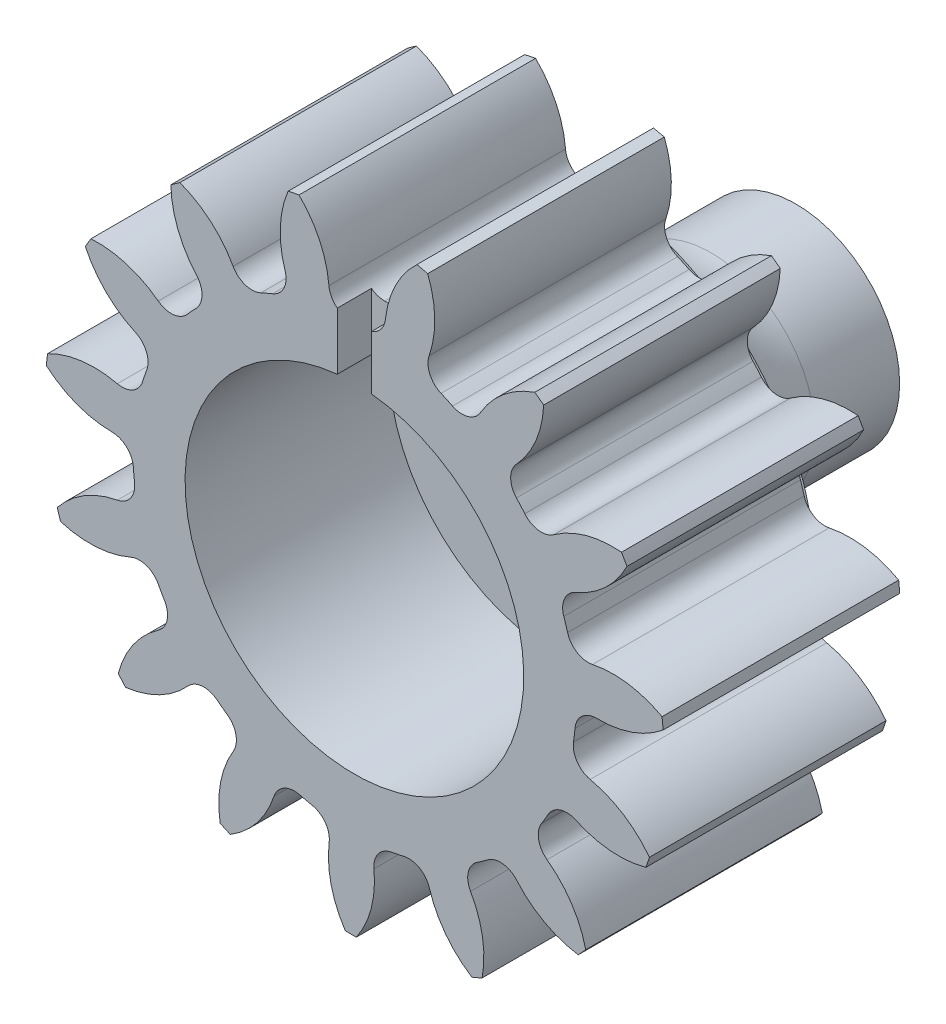
SolidWorks part; units mm, degrees
material "ABS"
ref_plane "Front" through (0, 0, 0) normal (0, 0, 1) x (1, 0, 0)
ref_plane "Top" through (0, 0, 0) normal (0, 1, 0) x (1, 0, 0)
ref_plane "Right" through (0, 0, 0) normal (1, 0, 0) x (0, 0, -1)
sketch "Sketch3" plane through (0, 0, 0) normal (0, 0, 1) x (1, 0, 0)
  circle A0 centre (0, 0) radius 21.59
  dimension "od" = 43.18
extrude "gearBody" add sketch "Sketch3" along normal blind 11
sketch "Sketch2" plane through (0, 0, 0) normal (0, 0, 1) x (1, 0, 0)
  line L0 (0, 0) -> (17.0393, 7.0579) construction
  line L1 (22.0105, -8.0941) -> (0, 0) construction
  line L2 (0, 0) -> (36.3143, 0) construction
  line L3 (19.0486, -0.229) -> (18.5878, -4.1711) construction
  line L5 (18.8182, -2.2) -> (0, 0) construction
  line L7 (0, 0) -> (18.4432, 0) construction
  arc A0 (18.4395, -0.3701) -> (18.0276, -3.8932) centre (0, 0) ccw construction
  arc A1 (21.5666, 1.0048) -> (20.7532, -5.9524) centre (0, 0) ccw construction
  arc A2 (19.0486, -0.229) -> (18.5878, -4.1711) centre (0, 0) ccw construction
  arc A3 (15.7838, -2.3046) -> (15.8898, -1.3984) centre (0, 0) ccw construction
  arc A4 (22.0105, -8.0941) -> (16.5506, -3.4102) centre (14.9518, -10.798) ccw construction
  arc A5 (22.0105, -8.0941) -> (23.2839, 2.7987) centre (0, 0) ccw construction
  arc A6 (23.2839, 2.7987) -> (16.8909, -0.4995) centre (17.0393, 7.0579) cw construction
  arc A7 (15.8898, -1.3984) -> (16.8909, -0.4995) centre (16.8715, -1.4848) cw construction
  arc A8 (16.5506, -3.4102) -> (15.7838, -2.3046) centre (16.759, -2.4469) cw construction
  arc A9 (23.5577, 4.3699) -> (16.9008, 0.0084) centre (17.0393, 7.0579) cw
  arc A10 (15.3837, -1.3539) -> (16.9008, 0.0084) centre (16.8715, -1.4848) cw
  arc A11 (15.2812, -2.2312) -> (15.3837, -1.3539) centre (0, 0) ccw
  arc A12 (16.4431, -3.9067) -> (15.2812, -2.2312) centre (16.759, -2.4469) cw
  arc A13 (21.9144, -9.686) -> (16.4431, -3.9067) centre (14.9518, -10.798) ccw
  arc A14 (21.9144, -9.686) -> (23.5577, 4.3699) centre (0, 0) ccw
  point P6 (23.2839, 2.7987)
  point P22 (22.0105, -8.0941)
  dimension "D1" = 0.508
  dimension "baseDia" = 36.8864
  dimension "od" = 43.18
  dimension "pd" = 38.1
  dimension "rd" = 31.9024
  dimension "rFillet" = 0.9855
  dimension "pointX" = 23.2839
  dimension "pointY" = 2.7987
  dimension "CTT" = 3.9421
  dimension "flankCenterAngle" = 22.5
extrude "toothCut" cut sketch "Sketch2" along normal through all
pattern_circular "CirPattern1" count 15 over 360 about axis through (0, 0, 0) along (0, 0, 1) of "toothCut"
scale "Scale1" scale about centroid uniform scaling no x scale factor 0.666667 y scale factor 0.666667 z scale factor 1
sketch "hub1Dia" plane through (0, 0, 0) normal (0, 0, -1) x (-1, 0, 0)
  circle A0 centre (0, 0) radius 12.7
  dimension "hub1Dia" = 25.4
sketch "hub2Dia" plane through (0, 0, 11) normal (0, 0, 1) x (1, 0, 0)
  circle A0 centre (0, 0) radius 12.7
  dimension "hub2dia" = 25.4
sketch "boreDia" plane through (0, 0, 0) normal (0, 0, 1) x (1, 0, 0)
  circle A0 centre (0, 0) radius 7.874
  dimension "boreDia" = 15.748
extrude "bore" cut sketch "boreDia" against normal mid plane 25400
sketch "Sketch4" plane through (0, 0, 0) normal (1, 0, 0) x (0, 0, -1)
  line L0 (9.525, 0) -> (-1.524, 0)
  line L1 (-1.524, 0) -> (-1.524, 7.874)
  line L2 (-1.524, 7.874) -> (0, 7.874)
  line L4 (0, 7.874) -> (0, 10.414)
  line L7 (5.588, 4.826) -> (9.525, 4.826)
  line L8 (9.525, 4.826) -> (9.525, 0)
  line L9 (0, 0) -> (18.4907, 0) construction
  line L11 (0, 8.3769) -> (0, 11.3894) construction
  arc A0 (0, 10.414) -> (5.588, 4.826) centre (5.588, 10.414) ccw
  point P10 (0, 0)
  point P13 (0, 0)
  dimension "D2" = 5.588
  dimension "D1" = 15.748
  dimension "D3" = 1.524
  dimension "D5" = 9.652
  dimension "D6" = 9.525
revolve "Revolve1" add sketch "Sketch4" angle 360 about L9
sketch "Sketch5" plane through (0, 0, -9.525) normal (0, 0, -1) x (-1, 0, 0)
  circle A0 centre (0, 0) radius 2.65
  dimension "D1" = 5.3
extrude "Cut-Extrude1" cut sketch "Sketch5" against normal blind 3.746
sketch "Sketch6" plane through (0, 0, -9.525) normal (0, 0, -1) x (-1, 0, 0)
  line L0 (0, 0) -> (0, 3.8857) construction
  line L1 (0.06, 3.0494) -> (0.23, 2.64)
  line L2 (-0.06, 3.0494) -> (-0.23, 2.64)
  circle A0 centre (0, 0) radius 2.65 construction
  arc A1 (0.23, 2.64) -> (-0.23, 2.64) centre (0, 0) ccw
  arc A2 (0.06, 3.0494) -> (-0.06, 3.0494) centre (0, 0) ccw
  dimension "D1" = 6.1
  dimension "D2" = 0.06
  dimension "D3" = 0.23
extrude "Cut-Extrude4" cut sketch "Sketch6" against normal blind 3.746
pattern_circular "CirPattern2" count 25 over 360 about axis through (0, 0, 0) along (0, 0, 1) of "Cut-Extrude4"
sketch "Sketch7" plane through (0, 0, 11) normal (0, 0, 1) x (1, 0, 0)
  line L1 (-0.7937, 13.1786) -> (0.7937, 13.1786)
  line L2 (-0.7937, 13.1786) -> (-0.7937, 5.7938)
  line L3 (-0.7937, 5.7938) -> (0.7937, 5.7938)
  line L4 (0.7937, 13.1786) -> (0.7937, 5.7938)
  point P4 (0, 5.7938)
  point P6 (0, 0)
  dimension "D1" = 1.5875
extrude "Cut-Extrude5" cut sketch "Sketch7" against normal blind 1.5875
equation "\"Motor_OD\" = 54.4mm"
equation "\"Motor_Length\" = 401mm"
equation "\"Aft_Section_Length\" = 32in"
equation "\"Mid_Coupler_Length\" = 12in"
equation "\"AB_Coupler_OD_Length\"= 1in"
equation "\"AB_Coupling_Section_Length\"= 0.375in"
equation "\"AB_Coupler_Length\"= \"AB_Coupler_OD_Length\" + \"AB_Coupling_Section_Length\" * 2"
equation "\"Cutout_Angle\" = 60"
equation "\"AB_Paddle_Height\" = 0.375in"
equation "\"AB_Coupler_Num_Screws\"= 4"
equation "\"Num_Cutouts\" = 4"
equation "\"AB_Coupler_OD\"= 4.024in"
equation "\"AB_Coupler_ID\"= 3.7in"
equation "\"AB_Coupler_Surface_Diameter\"= 3.899in"
equation "\"AB_Coupling_Screw_Diameter\"= 4.5mm"
equation "\"AB_Central_Bushing_Length\" = 0.75in"
equation "\"Lead_Screw_Dist\" = 2in"
equation "\"Lead_Screw_Diam\" = 0.375in"
equation "\"Lead_Screw_Length\" = \"Mid_Coupler_Length\" + 2*0.375in + 2*0.5in"
equation "\"Paddle_Pin_Offset\" = 0.25in"
equation "\"Paddle_Pin_Radius\" = 2.25*2/3in"
equation "\"Paddle_Gear_OD\" = 3.2in"
equation "\"Fwd_BKHD_From_Top\" = 18in"
equation "\"Body_Tube_OD\"= 4.024in"
equation "\"Body_Tube_ID\"= 3.90in"
equation "\"Coupler_OD\" = 3.899in"
equation "\"Coupler_ID\" = 3.755in"
equation "\"Fwd_Section_Length\" = 20in"
equation "\"Mid_Section_Length\" = 4in"
equation "\"Aft_Upper_Tube_Length\" = 10in"
equation "\"Aft_Lower_Tube_Length\" = 18in"
equation "\"Nosecone_Coupler_Length\" = 5in"
equation "\"Avionics_Bulkhead_Thickness\" = 0.25in"
equation "\"Avionics_Bulkhead_Lip\" = 0.125in"
equation "\"Avionics_Board_Length\" = \"Mid_Coupler_Length\" - 2*\"Avionics_Bulkhead_Lip\""
equation "\"Lead_Screw_Hole_Diam\" = 0.386in"
equation "\"Centering_Ring_Cutout_Dia\"= 1in"
equation "\"Fin_Thickness\" = 0.118in"
equation "\"Airbrakes_Wire_Hole_Dist\" = 1.1*2/3in"
equation "\"Airbrakes_Wire_Hole_Dia\" = 0.25in"
equation "\"Drive_Gear_OD\" = 1.7*2/3in"
equation "\"DB9_Hole_Dist\" = 25mm"
equation "\"DB9_Relief_Width\" = 0.47in"
equation "\"DB9_Relief_Hole_Offset\" = 0.09in"
equation "\"Servo_Gear_Offset\" = 0.5in"
equation "\"Mounting_Bracket_Centerhole_DIA\" = 0.4in"
equation "\"Drive_Gear_Shaft_DIA\" = \"Mounting_Bracket_Centerhole_DIA\" - 0.02in"
equation "\"Drive_Gear_Fillet\" = 0.22in"
equation "\"Drive_Gear_ID\" = 0.62in"
equation "\"M3_Thread_Clearance\" = 3.8mm"
equation "\"M3_Screw_Head_Diam\" = 6.5mm"
equation "\"Screw_Angle\" = 12.5deg"
equation "\"M3_Insert_OD\" = 4.1mm"
equation "\"M4_Insert_OD\" = 5.5mm"
equation "\"Mounting_Hole_Dist\" = 0.15in"
equation "\"Cam_Slot_Length\" = 7mm"
equation "\"Cam_Slot_Width\" = 10mm"
equation "\"D2@Sketch4\"=\"Drive_Gear_Fillet\""
equation "\"D5@Sketch4\"=\"Drive_Gear_Shaft_DIA\""
equation "\"D1@Sketch4\"=\"Drive_Gear_ID\""
equation "\"Drive_Gear_Offset\" = 0.01in"
